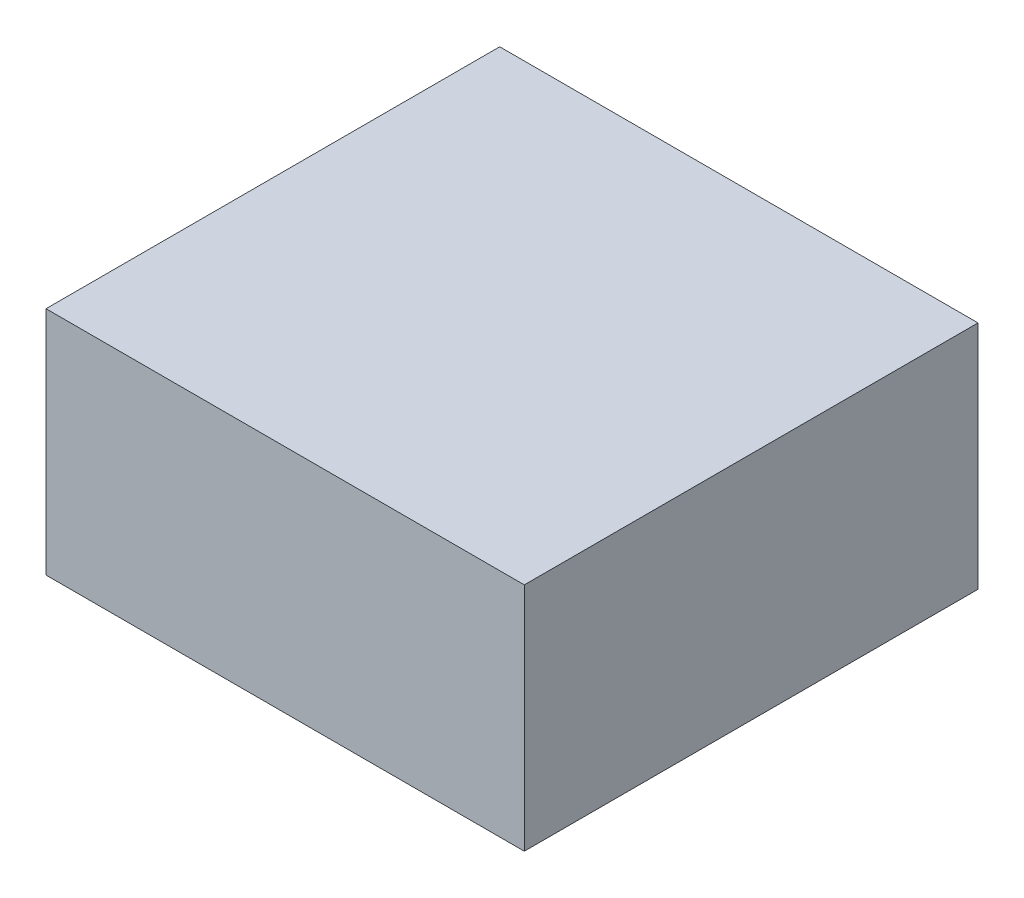
SolidWorks part; units mm, degrees
ref_plane "Front Plane" through (0, 0, 0) normal (0, 0, 1) x (1, 0, 0)
ref_plane "Top Plane" through (0, 0, 0) normal (0, 1, 0) x (1, 0, 0)
ref_plane "Right Plane" through (0, 0, 0) normal (1, 0, 0) x (0, 0, -1)
sketch "Sketch1" plane through (0, 0, 0) normal (0, 0, 1) x (1, 0, 0)
  line L1 (-39.497, -19.05) -> (39.497, -19.05)
  line L2 (-39.497, -19.05) -> (-39.497, 19.05)
  line L3 (-39.497, 19.05) -> (39.497, 19.05)
  line L4 (39.497, -19.05) -> (39.497, 19.05)
  line L5 (-39.497, -19.05) -> (39.497, 19.05) construction
  line L6 (-39.497, 19.05) -> (39.497, -19.05) construction
  point P1 (0, 0)
  dimension "D1" = 78.994
  dimension "D2" = 38.1
extrude "Boss-Extrude1" add sketch "Sketch1" along normal blind 74.93
ref_point "Point1"
